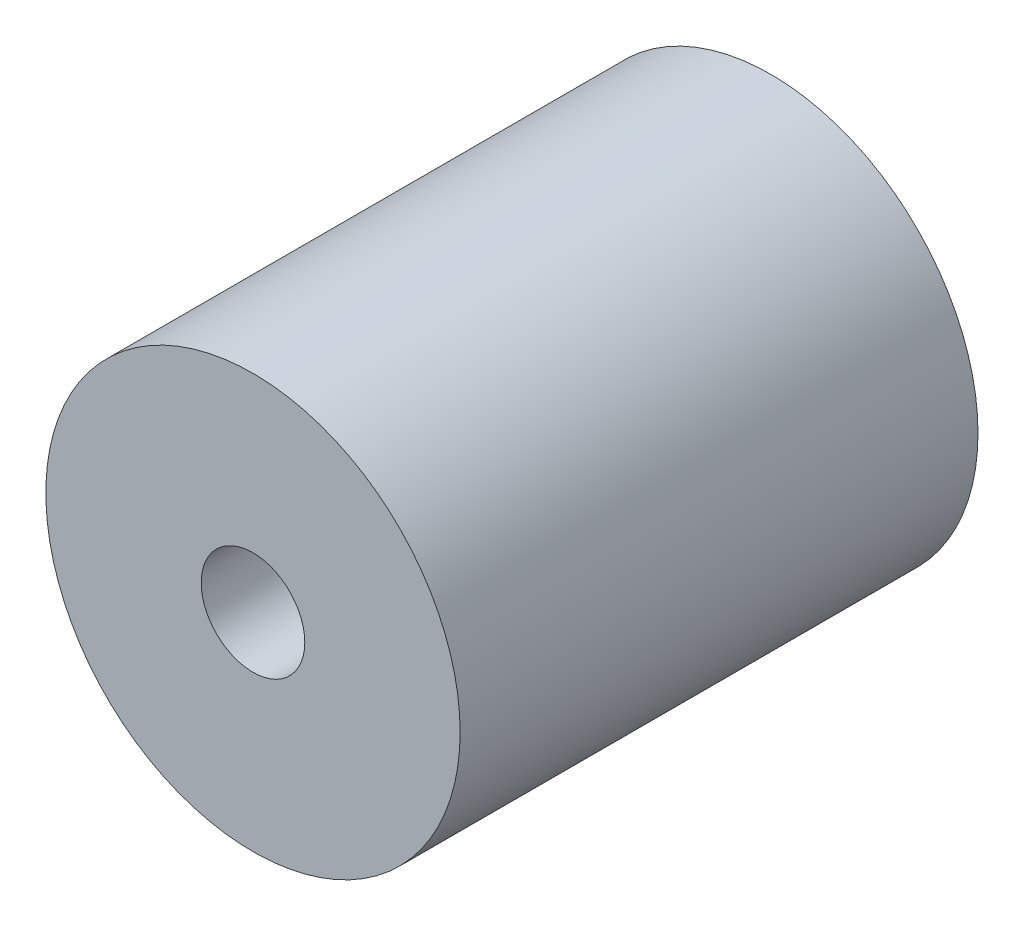
SolidWorks part; units mm, degrees
material "6061 Alloy"
ref_plane "Front Plane" through (0, 0, 0) normal (0, 0, 1) x (1, 0, 0)
ref_plane "Top Plane" through (0, 0, 0) normal (0, 1, 0) x (1, 0, 0)
ref_plane "Right Plane" through (0, 0, 0) normal (1, 0, 0) x (0, 0, -1)
sketch "Sketch1" plane through (0, 0, 0) normal (0, 0, 1) x (1, 0, 0)
  circle A0 centre (0, 0) radius 10
  dimension "D1" = 20
extrude "Boss-Extrude1" add sketch "Sketch1" along normal blind 25
sketch "Sketch2" plane through (0, 0, 25) normal (0, 0, 1) x (1, 0, 0)
  circle A0 centre (0, 0) radius 2.5
  dimension "D1" = 5
extrude "Cut-Extrude1" cut sketch "Sketch2" against normal blind 10
sketch "Sketch3" plane through (0, 0, 0) normal (0, 0, -1) x (-1, 0, 0)
  circle A0 centre (0, 0) radius 4
  dimension "D1" = 8
extrude "Cut-Extrude2" cut sketch "Sketch3" against normal blind 10
